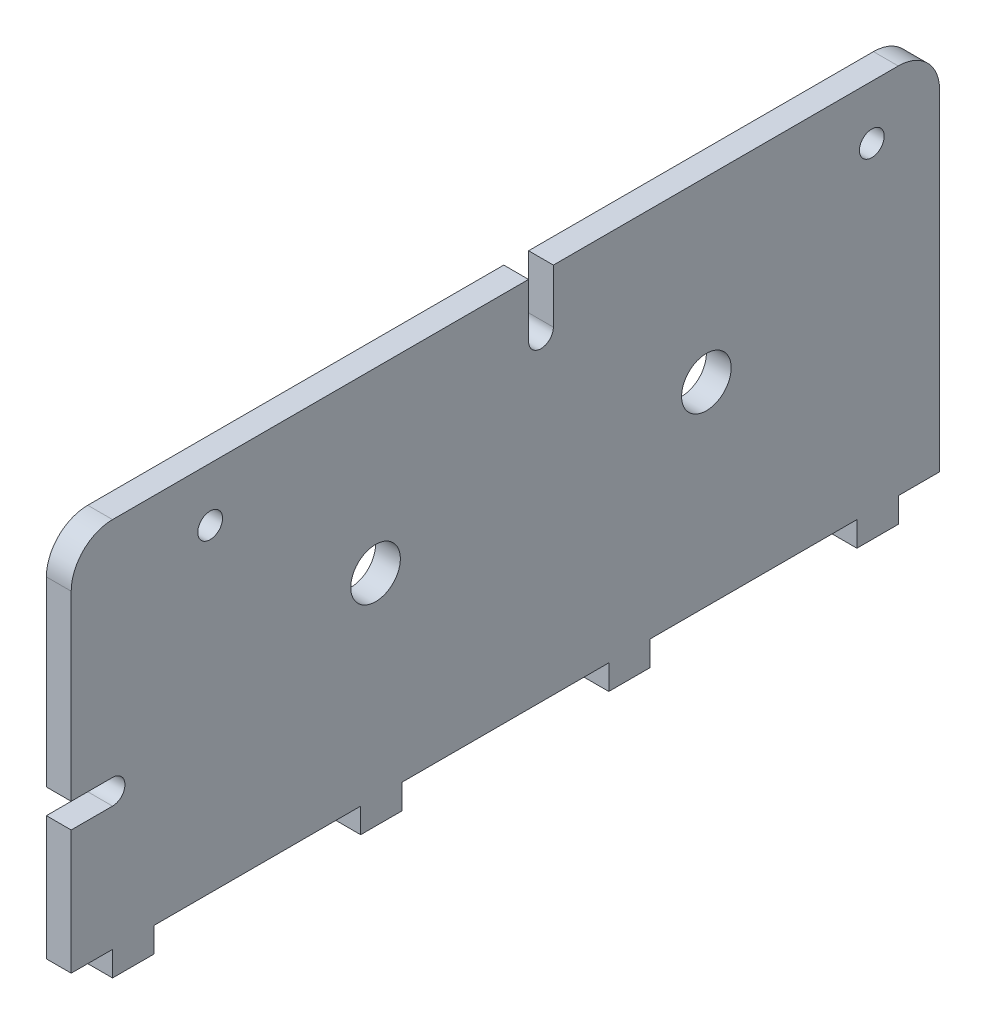
SolidWorks part; units mm, degrees
ref_plane "Front Plane" through (0, 0, 0) normal (0, 0, 1) x (1, 0, 0)
ref_plane "Top Plane" through (0, 0, 0) normal (0, 1, 0) x (1, 0, 0)
ref_plane "Right Plane" through (0, 0, 0) normal (1, 0, 0) x (0, 0, -1)
sketch "Sketch1" plane through (0, 0, 0) normal (1, 0, 0) x (0, 0, -1)
  line L1 (75, 0) -> (-30, 0)
  line L2 (75, 0) -> (75, 45)
  line L3 (75, 45) -> (-30, 45)
  line L4 (-30, 0) -> (-30, 45)
  line L5 (55, 0) -> (-55, 0) construction
  point P0 (0, 0)
  dimension "D2" = 30
  dimension "D1" = 105
  dimension "D4" = 45
extrude "Boss-Extrude1" add sketch "Sketch1" along normal blind 3
sketch "Sketch2" plane through (3, 0, 0) normal (1, 0, 0) x (0, 0, -1)
  line L0 (-30, 0) -> (75, 0) construction
  line L1 (-30, 45) -> (-30, 0) construction
  line L7 (-26.9862, 0) -> (-28.4862, -10) construction
  line L8 (25.3, 38.5) -> (25.3, 45)
  line L9 (75, 45) -> (-30, 45) construction
  line L11 (28.3, 38.5) -> (28.3, 45)
  line L12 (28.3, 45) -> (25.3, 45)
  circle A0 centre (6.8, 23.5) radius 3
  circle A1 centre (46.8, 23.5) radius 3
  arc A3 (25.3, 38.5) -> (28.3, 38.5) centre (26.8, 38.5) ccw
  circle A4 centre (66.8, 38.5) radius 1.5
  circle A6 centre (-13.2, 38.5) radius 1.5
  point P6 (-28.4862, -10)
  point P11 (28.0724, -10)
  dimension "D1" = 6
  dimension "D3" = 36.8
  dimension "D4" = 6
  dimension "D7" = 3
  dimension "D11" = 3
  dimension "D14" = 3
  dimension "D2" = 23.5
  dimension "D5" = 40
  dimension "D8" = 15
  dimension "D10" = 20
  dimension "D15" = 20
  dimension "D17" = 20
extrude "Cut-Extrude1" cut sketch "Sketch2" against normal through all
sketch "Sketch3" plane through (3, 0, 0) normal (1, 0, 0) x (0, 0, -1)
  line L0 (-30, 45) -> (-30, 0) construction
  line L1 (-25, 15) -> (-30, 15)
  line L3 (-25, 18) -> (-30, 18)
  line L4 (-30, 15) -> (-30, 18)
  line L5 (-30, 0) -> (75, 0) construction
  arc A0 (-25, 15) -> (-25, 18) centre (-25, 16.5) ccw
  dimension "D1" = 1.5
  dimension "D2" = 15
  dimension "D3" = 5
extrude "Cut-Extrude2" cut sketch "Sketch3" against normal through all
ref_plane "Plane2" through (0, 22.25, 0) normal (0, -1, 0) x (-1, 0, 0)
ref_plane "Plane3" through (0, 0, -75) normal (0, 0, -1) x (-1, 0, 0)
fillet "Fillet3" radius 5 2 edges at (1.5, 45, -75) (1.5, 45, 30)
ref_plane "Plane4" through (0, 0, -22.5) normal (0, 0, 1) x (1, 0, 0)
sketch "Sketch4" plane through (0, 0, 0) normal (0, 1, 0) x (1, 0, 0)
  line L0 (3, -30) -> (3, 75) construction
  line L1 (3, -25) -> (0, -25)
  line L2 (3, -25) -> (3, -20)
  line L3 (3, -20) -> (0, -20)
  line L4 (0, -25) -> (0, -20)
  line L5 (0, -30) -> (0, 75) construction
  line L6 (3, -30) -> (0, -30) construction
  dimension "D1" = 5
  dimension "D2" = 5
extrude "Boss-Extrude2" add sketch "Sketch4" against normal blind 3
pattern_linear "LPattern1" count 4 spacing 30 along (0, 0, -1) of "Boss-Extrude2"
